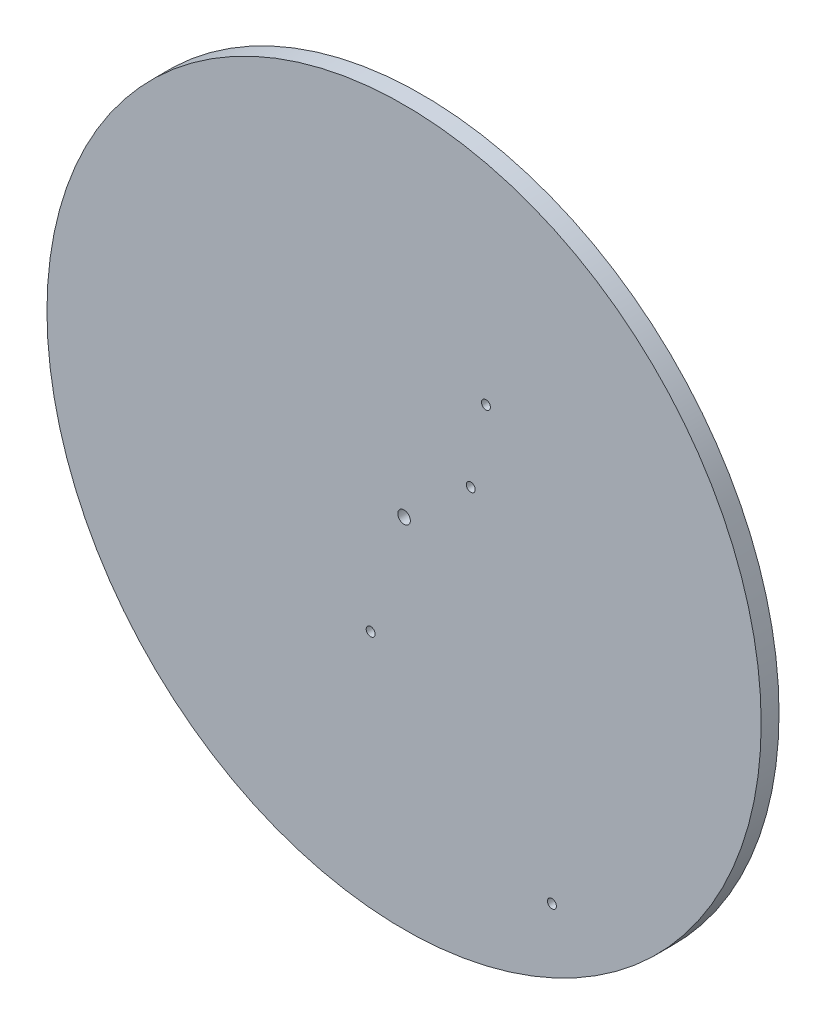
SolidWorks part; units mm, degrees
ref_plane "Front Plane" through (0, 0, 0) normal (0, 0, 1) x (1, 0, 0)
ref_plane "Top Plane" through (0, 0, 0) normal (0, 1, 0) x (1, 0, 0)
ref_plane "Right Plane" through (0, 0, 0) normal (1, 0, 0) x (0, 0, -1)
sketch "Sketch1" plane through (0, 0, 0) normal (0, 0, 1) x (1, 0, 0)
  circle A0 centre (0, 0) radius 200
  circle A1 centre (0, 0) radius 3.5
  dimension "D1" = 400
  dimension "D2" = 7
extrude "Boss-Extrude1" add sketch "Sketch1" along normal blind 10
sketch "Sketch2" plane through (0, 0, 10) normal (0, 0, 1) x (1, 0, 0)
  circle A0 centre (37.34, 33.25) radius 2.5
  circle A1 centre (45.86, 77.44) radius 2.5
  dimension "D1" = 5
  dimension "D2" = 37.34
  dimension "D3" = 33.25
  dimension "D4" = 77.44
  dimension "D5" = 45.86
extrude "Cut-Extrude1" cut sketch "Sketch2" against normal through all
sketch "Sketch3" plane through (0, 0, 10) normal (0, 0, 1) x (1, 0, 0)
  circle A0 centre (-18.71, -64.86) radius 2.5
  dimension "D1" = 5
  dimension "D2" = 64.86
  dimension "D3" = 18.71
extrude "Cut-Extrude2" cut sketch "Sketch3" against normal through all
sketch "Sketch4" plane through (0, 0, 10) normal (0, 0, 1) x (1, 0, 0)
  circle A0 centre (82.82, -146.05) radius 2.5
  dimension "D3" = 5
  dimension "D1" = 82.82
  dimension "D2" = 146.05
extrude "Cut-Extrude3" cut sketch "Sketch4" against normal through all
